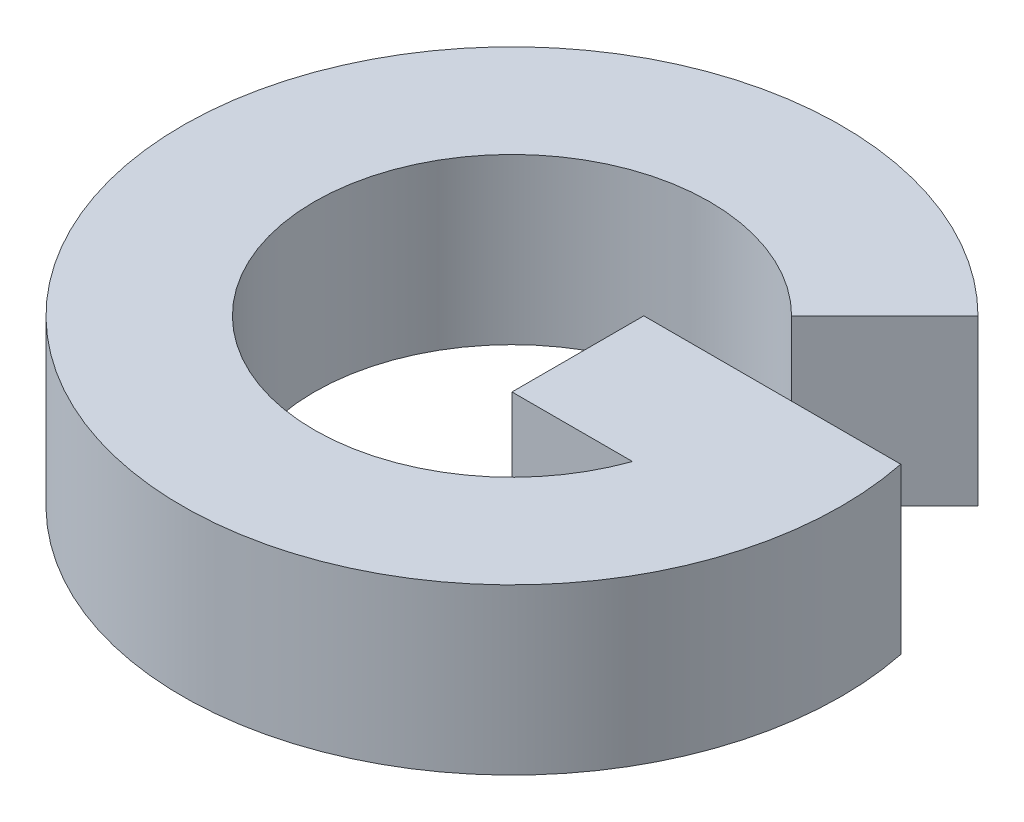
SolidWorks part; units mm, degrees
ref_plane "Front Plane" through (0, 0, 0) normal (0, 0, 1) x (1, 0, 0)
ref_plane "Top Plane" through (0, 0, 0) normal (0, 1, 0) x (1, 0, 0)
ref_plane "Right Plane" through (0, 0, 0) normal (1, 0, 0) x (0, 0, -1)
sketch "Sketch1" plane through (0, 0, 0) normal (0, 1, 0) x (1, 0, 0)
  line L0 (320, 20) -> (320, 0) construction
  line L1 (328.4853, 28.4853) -> (334.1421, 34.1421)
  line L2 (320, 20) -> (340, 20) construction
  line L3 (324, 24) -> (339.5959, 24)
  line L4 (324, 16) -> (331.3137, 16)
  line L5 (324, 16) -> (324, 24)
  arc A0 (334.1421, 34.1421) -> (339.5959, 24) centre (320, 20) ccw
  arc A1 (328.4853, 28.4853) -> (331.3137, 16) centre (320, 20) ccw
  point P6 (0, 0)
  dimension "D1" = 300
  dimension "D2" = 40
  dimension "D3" = 24
  dimension "D4" = 4
  dimension "D5" = 8
  dimension "D6" = 45
  dimension "D7" = 4
extrude "Boss-Extrude1" add sketch "Sketch1" along normal blind 10
